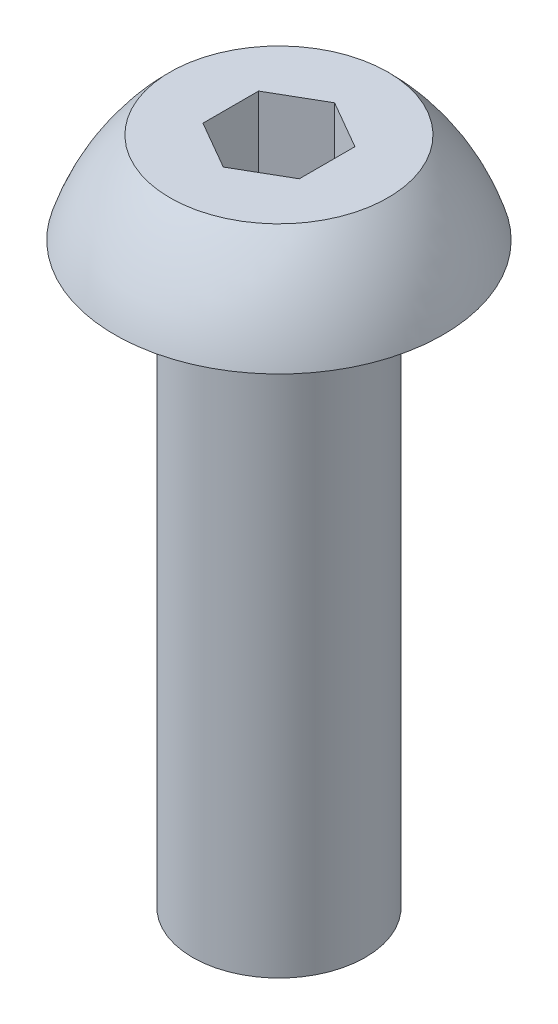
SolidWorks part; units mm, degrees
material "AISI Type 316L stainless steel"
ref_plane "Front Plane" through (0, 0, 0) normal (0, 0, 1) x (1, 0, 0)
ref_plane "Top Plane" through (0, 0, 0) normal (0, 1, 0) x (1, 0, 0)
ref_plane "Right Plane" through (0, 0, 0) normal (1, 0, 0) x (0, 0, -1)
sketch "Sketch1" plane through (0, 0, 0) normal (0, 0, 1) x (1, 0, 0)
  line L0 (-1.4224, 0) -> (-2.7051, 0)
  line L1 (-1.4224, 0) -> (-1.4224, -9.525)
  line L2 (0, -9.525) -> (0, 1.4986)
  line L3 (0, 1.4986) -> (-1.7948, 1.4986)
  line L4 (-1.4224, -9.525) -> (0, -9.525)
  arc A0 (-2.7051, 0) -> (-1.7948, 1.4986) centre (0.7001, -1.0427) cw
  dimension "D1" = 9.525
  dimension "D2" = 1.4986
  dimension "D3" = 2.7051
  dimension "D4" = 1.4224
  dimension "D5" = 1.7948
revolve "Revolve1" add sketch "Sketch1" angle 360 about L2
sketch "Sketch2" plane through (0, 1.4986, 0) normal (0, 1, 0) x (1, 0, 0)
  line L0 (0, 0) -> (0, 0.9165) construction
  line L1 (-0.7938, 0.4583) -> (-0.7937, -0.4583)
  line L2 (-0.7937, -0.4583) -> (0, -0.9165)
  line L3 (0, -0.9165) -> (0.7937, -0.4583)
  line L4 (0.7937, -0.4583) -> (0.7937, 0.4583)
  line L5 (0.7937, 0.4583) -> (0, 0.9165)
  line L6 (0, 0.9165) -> (-0.7938, 0.4583)
  circle A0 centre (0, 0) radius 0.7937 construction
  dimension "D1" = 1.5875
extrude "Cut-Extrude1" cut sketch "Sketch2" against normal blind 1.27
